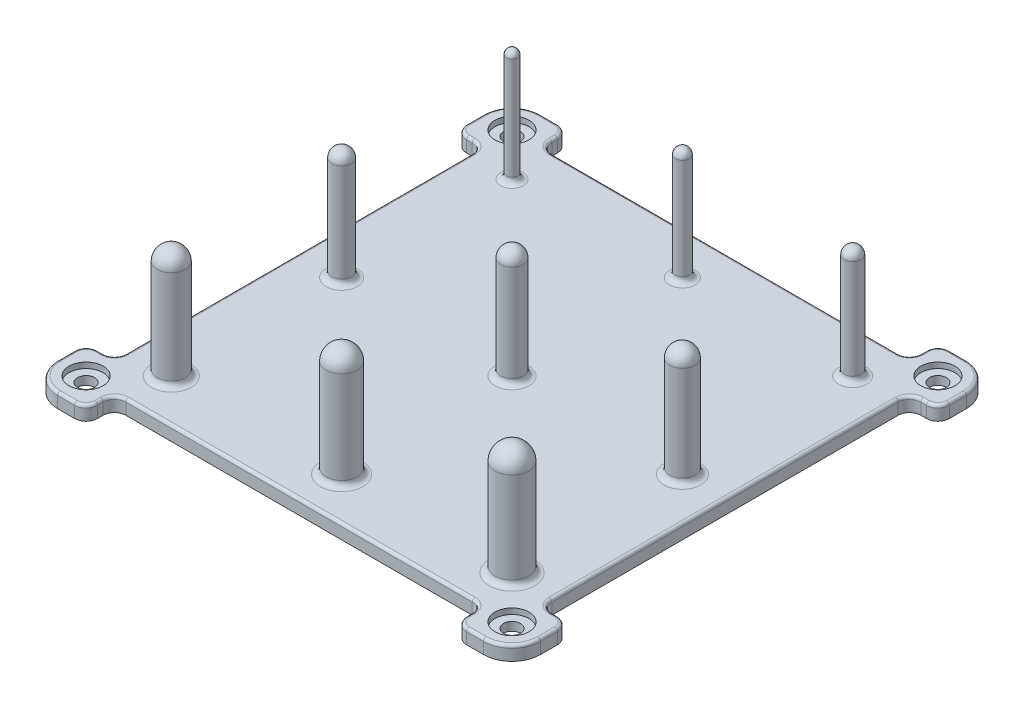
SolidWorks part; units mm, degrees
ref_plane "Front Plane" through (0, 0, 0) normal (0, 0, 1) x (1, 0, 0)
ref_plane "Top Plane" through (0, 0, 0) normal (0, 1, 0) x (1, 0, 0)
ref_plane "Right Plane" through (0, 0, 0) normal (1, 0, 0) x (0, 0, -1)
sketch "Sketch2" plane through (0, 0, 0) normal (0, 1, 0) x (1, 0, 0)
  line L1 (-78.2519, 33.644) -> (71.7481, 33.644)
  line L2 (-88.2519, 23.644) -> (-88.2519, -126.356)
  line L3 (-78.2519, -136.356) -> (71.7481, -136.356)
  line L4 (81.7481, 23.644) -> (81.7481, -126.356)
  arc A0 (-88.2519, -126.356) -> (-78.2519, -136.356) centre (-78.2519, -126.356) ccw
  arc A1 (71.7481, -136.356) -> (81.7481, -126.356) centre (71.7481, -126.356) ccw
  arc A2 (71.7481, 33.644) -> (81.7481, 23.644) centre (71.7481, 23.644) cw
  arc A3 (-78.2519, 33.644) -> (-88.2519, 23.644) centre (-78.2519, 23.644) ccw
  point P8 (81.7481, -136.356)
  point P11 (81.7481, 33.644)
  point P14 (-88.2519, 33.644)
  dimension "D3" = 10
  dimension "D1" = 170
  dimension "D2" = 170
extrude "Boss-Extrude1" add sketch "Sketch2" along normal blind 5
sketch "Sketch3" plane through (0, 5, 0) normal (0, 1, 0) x (1, 0, 0)
  line L0 (71.7481, 33.644) -> (-78.2519, 33.644) construction
  line L1 (-88.2519, 23.644) -> (-88.2519, -126.356) construction
  line L2 (81.7481, -126.356) -> (81.7481, 23.644) construction
  line L3 (-78.2519, -136.356) -> (71.7481, -136.356) construction
  circle A0 centre (71.7481, 23.644) radius 6
  circle A1 centre (71.7481, -126.356) radius 6
  circle A2 centre (-78.2519, 23.644) radius 6
  circle A3 centre (-78.2519, -126.356) radius 6
  dimension "D1" = 10
  dimension "D2" = 10
  dimension "D3" = 10
  dimension "D4" = 10
  dimension "D5" = 10
  dimension "D6" = 10
  dimension "D7" = 10
  dimension "D8" = 10
  dimension "D10" = 150
extrude "Cut-Extrude1" cut sketch "Sketch3" against normal blind 2 contours A3 | A1 | A0 | A2
sketch "Sketch9" plane through (0, 5, 0) normal (0, 1, 0) x (1, 0, 0)
  line L0 (-78.2519, -136.356) -> (71.7481, -136.356) construction
  line L1 (-88.2519, 23.644) -> (-88.2519, -126.356) construction
  line L2 (81.7481, -126.356) -> (81.7481, 23.644) construction
  line L3 (71.7481, 33.644) -> (-78.2519, 33.644) construction
  circle A0 centre (-78.2519, 23.644) radius 3
  circle A1 centre (71.7481, 23.644) radius 3
  circle A2 centre (71.7481, -126.356) radius 3
  circle A3 centre (-78.2519, -126.356) radius 3
  dimension "D1" = 10
  dimension "D2" = 10
  dimension "D3" = 10
  dimension "D4" = 10
  dimension "D5" = 10
  dimension "D6" = 10
  dimension "D7" = 10
  dimension "D8" = 10
extrude "Cut-Extrude4" cut sketch "Sketch9" against normal through all
sketch "Sketch10" plane through (0, 5, 0) normal (0, 1, 0) x (1, 0, 0)
  line L4 (71.7481, 33.644) -> (-78.2519, 33.644) construction
  line L5 (-88.2519, 23.644) -> (-88.2519, -126.356) construction
  line L7 (81.7481, -126.356) -> (81.7481, 23.644) construction
  line L8 (-78.2519, -136.356) -> (71.7481, -136.356) construction
  circle A0 centre (-63.2519, 8.644) radius 2
  circle A1 centre (-3.2519, 8.644) radius 2.5
  circle A2 centre (56.7481, 8.644) radius 3
  circle A3 centre (-63.2519, -51.356) radius 3.5
  circle A4 centre (-3.2519, -51.356) radius 4
  circle A5 centre (56.7481, -51.356) radius 4.5
  circle A6 centre (-63.2519, -111.356) radius 5
  circle A7 centre (-3.2519, -111.356) radius 5.5
  circle A8 centre (56.7481, -111.356) radius 6
  dimension "D1" = 60
  dimension "D2" = 60
  dimension "D3" = 60
  dimension "D4" = 60
  dimension "D5" = 60
  dimension "D6" = 60
  dimension "D7" = 60
  dimension "D8" = 60
  dimension "D9" = 60
  dimension "D10" = 60
  dimension "D11" = 60
  dimension "D12" = 60
  dimension "D13" = 25
  dimension "D14" = 25
  dimension "D15" = 25
  dimension "D16" = 25
  dimension "D17" = 25
  dimension "D18" = 25
  dimension "D19" = 25
  dimension "D20" = 25
extrude "Boss-Extrude6" add sketch "Sketch10" along normal blind 40
fillet "Fillet1" radius 2 1 edges at (-63.2519, 45, -6.644)
fillet "Fillet2" radius 2.5 1 edges at (-3.2519, 45, -6.144)
fillet "Fillet3" radius 3 1 edges at (56.7481, 45, -5.644)
fillet "Fillet4" radius 3.5 1 edges at (-63.2519, 45, 54.856)
fillet "Fillet5" radius 4 1 edges at (-3.2519, 45, 55.356)
fillet "Fillet6" radius 4.5 1 edges at (56.7481, 45, 55.856)
fillet "Fillet7" radius 5 1 edges at (-63.2519, 45, 116.356)
fillet "Fillet8" radius 5.5 1 edges at (-3.2519, 45, 116.856)
fillet "Fillet9" radius 6 1 edges at (56.7481, 45, 117.356)
fillet "Fillet11" radius 2 1 edges at (-63.2519, 5, -6.644)
fillet "Fillet12" radius 2 1 edges at (-3.2519, 5, -6.144)
fillet "Fillet13" radius 2 1 edges at (56.7481, 5, -5.644)
fillet "Fillet14" radius 2 1 edges at (-63.2519, 5, 54.856)
fillet "Fillet15" radius 2 1 edges at (-3.2519, 5, 55.356)
fillet "Fillet16" radius 2 1 edges at (56.7481, 5, 55.856)
fillet "Fillet17" radius 2 1 edges at (-63.2519, 5, 116.356)
fillet "Fillet18" radius 2 1 edges at (-3.2519, 5, 116.856)
fillet "Fillet19" radius 2 1 edges at (56.7481, 5, 117.356)
sketch "Sketch12" plane through (0, 5, 0) normal (0, 1, 0) x (1, 0, 0)
  line L0 (-64.2519, 23.644) -> (57.7481, 23.644)
  line L1 (-78.2519, 9.644) -> (-78.2519, -112.356)
  line L2 (-64.2519, -126.356) -> (57.7481, -126.356)
  line L3 (71.7481, -112.356) -> (71.7481, 9.644)
  line L4 (-88.2519, 23.644) -> (-88.2519, -126.356) construction
  line L5 (81.7481, -126.356) -> (81.7481, 23.644) construction
  line L6 (71.7481, 33.644) -> (-78.2519, 33.644) construction
  line L7 (-78.2519, -136.356) -> (71.7481, -136.356) construction
  line L8 (-68.2519, 27.644) -> (-68.2519, 29.644)
  line L9 (-72.2519, 33.644) -> (-78.2519, 33.644)
  line L10 (-78.2519, 33.644) -> (-88.2519, 33.644)
  line L11 (-88.2519, 33.644) -> (-88.2519, 23.644)
  line L12 (-88.2519, 23.644) -> (-88.2519, 17.644)
  line L13 (-84.2519, 13.644) -> (-82.2519, 13.644)
  line L14 (61.7481, 27.644) -> (61.7481, 29.644)
  line L15 (65.7481, 33.644) -> (71.7481, 33.644)
  line L16 (71.7481, 33.644) -> (81.7492, 33.644)
  line L17 (81.7492, 33.644) -> (81.7481, 23.644)
  line L18 (81.7481, 23.644) -> (81.7481, 17.644)
  line L19 (77.7481, 13.644) -> (75.7481, 13.644)
  line L20 (75.7481, -116.356) -> (77.7481, -116.356)
  line L21 (81.7481, -120.356) -> (81.7481, -126.356)
  line L22 (81.7481, -126.356) -> (81.7481, -136.356)
  line L23 (81.7481, -136.356) -> (71.7481, -136.356)
  line L24 (71.7481, -136.356) -> (65.7481, -136.356)
  line L25 (61.7481, -132.356) -> (61.7481, -130.356)
  line L26 (-68.2519, -130.356) -> (-68.2519, -132.356)
  line L27 (-72.2519, -136.356) -> (-78.2519, -136.356)
  line L28 (-78.2519, -136.356) -> (-88.2519, -136.356)
  line L29 (-88.2519, -136.356) -> (-88.2519, -126.356)
  line L30 (-88.2519, -126.356) -> (-88.2519, -120.356)
  line L31 (-84.2519, -116.356) -> (-82.2519, -116.356)
  arc A0 (71.7481, -136.356) -> (81.7481, -126.356) centre (71.7481, -126.356) ccw construction
  arc A1 (-88.2519, 17.644) -> (-84.2519, 13.644) centre (-84.2519, 17.644) ccw
  arc A2 (-78.2519, 9.644) -> (-82.2519, 13.644) centre (-82.2519, 9.644) ccw
  arc A3 (-78.2519, -112.356) -> (-82.2519, -116.356) centre (-82.2519, -112.356) cw
  arc A4 (-88.2519, -120.356) -> (-84.2519, -116.356) centre (-84.2519, -120.356) cw
  arc A5 (-68.2519, -132.356) -> (-72.2519, -136.356) centre (-72.2519, -132.356) cw
  arc A6 (-64.2519, -126.356) -> (-68.2519, -130.356) centre (-64.2519, -130.356) ccw
  arc A7 (57.7481, -126.356) -> (61.7481, -130.356) centre (57.7481, -130.356) cw
  arc A8 (65.7481, -136.356) -> (61.7481, -132.356) centre (65.7481, -132.356) cw
  arc A9 (77.7481, -116.356) -> (81.7481, -120.356) centre (77.7481, -120.356) cw
  arc A10 (71.7481, -112.356) -> (75.7481, -116.356) centre (75.7481, -112.356) ccw
  arc A11 (71.7481, 9.644) -> (75.7481, 13.644) centre (75.7481, 9.644) cw
  arc A12 (81.7481, 17.644) -> (77.7481, 13.644) centre (77.7481, 17.644) cw
  arc A13 (61.7481, 29.644) -> (65.7481, 33.644) centre (65.7481, 29.644) cw
  arc A14 (57.7481, 23.644) -> (61.7481, 27.644) centre (57.7481, 27.644) ccw
  arc A15 (-64.2519, 23.644) -> (-68.2519, 27.644) centre (-64.2519, 27.644) cw
  arc A16 (-68.2519, 29.644) -> (-72.2519, 33.644) centre (-72.2519, 29.644) ccw
  point P49 (-88.2519, 13.644)
  point P52 (-78.2519, 13.644)
  point P55 (-78.2519, -116.356)
  point P58 (-88.2519, -116.356)
  point P61 (-68.2519, -136.356)
  point P64 (-68.2519, -126.356)
  point P67 (61.7481, -126.356)
  point P70 (61.7481, -136.356)
  point P73 (81.7481, -116.356)
  point P76 (71.7481, -116.356)
  point P79 (71.7481, 13.644)
  point P82 (81.7481, 13.644)
  point P85 (61.7481, 33.644)
  point P88 (61.7481, 23.644)
  point P91 (-68.2519, 23.644)
  point P94 (-68.2519, 33.644)
  dimension "D38" = 4
  dimension "D1" = 130
  dimension "D2" = 130
  dimension "D3" = 130
  dimension "D4" = 130
  dimension "D5" = 20
  dimension "D6" = 20
  dimension "D7" = 10
  dimension "D8" = 10
  dimension "D9" = 20
  dimension "D10" = 20
  dimension "D11" = 10
  dimension "10" = 10
  dimension "D12" = 20
  dimension "D13" = 20
  dimension "D14" = 20
  dimension "D15" = 10
  dimension "D16" = 10
  dimension "D17" = 10
  dimension "D18" = 10
  dimension "D19" = 10
  dimension "D20" = 10
  dimension "D21" = 10
  dimension "D22" = 10.0012
  dimension "D23" = 10
  dimension "D24" = 10
  dimension "D25" = 10
  dimension "D26" = 10
  dimension "D27" = 10
  dimension "D28" = 10
  dimension "D29" = 10
  dimension "D30" = 10
  dimension "D31" = 10
  dimension "D32" = 10
  dimension "D33" = 10
  dimension "D34" = 10
  dimension "D35" = 10
  dimension "D36" = 10
  dimension "D37" = 10
extrude "Cut-Extrude5" cut sketch "Sketch12" against normal blind 40 flip side to cut
fillet "Fillet20" radius 1 40 edges at (60.5765, 5, -24.8155) (61.7481, 5, -28.644) (62.9196, 5, -32.4724) (68.7481, 5, -33.644) (78.8191, 5, -30.715) (81.7481, 5, -20.644) (80.5765, 5, -14.8155) (76.7481, 5, -13.644) (72.9196, 5, -12.4724) (71.7481, 5, 51.356) (72.9196, 5, 115.1845) (76.7481, 5, 116.356) (80.5765, 5, 117.5276) (81.7481, 5, 123.356) (78.8191, 5, 133.4271) (68.7481, 5, 136.356) (62.9196, 5, 135.1845) (61.7481, 5, 131.356) (60.5765, 5, 127.5276) (-3.2519, 5, 126.356) (-67.0804, 5, 127.5276) (-68.2519, 5, 131.356) (-69.4235, 5, 135.1845) (-75.2519, 5, 136.356) (-85.323, 5, 133.4271) (-88.2519, 5, 123.356) (-87.0804, 5, 117.5276) (-83.2519, 5, 116.356) (-79.4235, 5, 115.1845) (-78.2519, 5, 51.356) (-79.4235, 5, -12.4724) (-83.2519, 5, -13.644) (-87.0804, 5, -14.8155) (-88.2519, 5, -20.644) (-85.323, 5, -30.715) (-75.2519, 5, -33.644) (-69.4235, 5, -32.4724) (-68.2519, 5, -28.644) (-67.0804, 5, -24.8155) (-3.2519, 5, -23.644)
